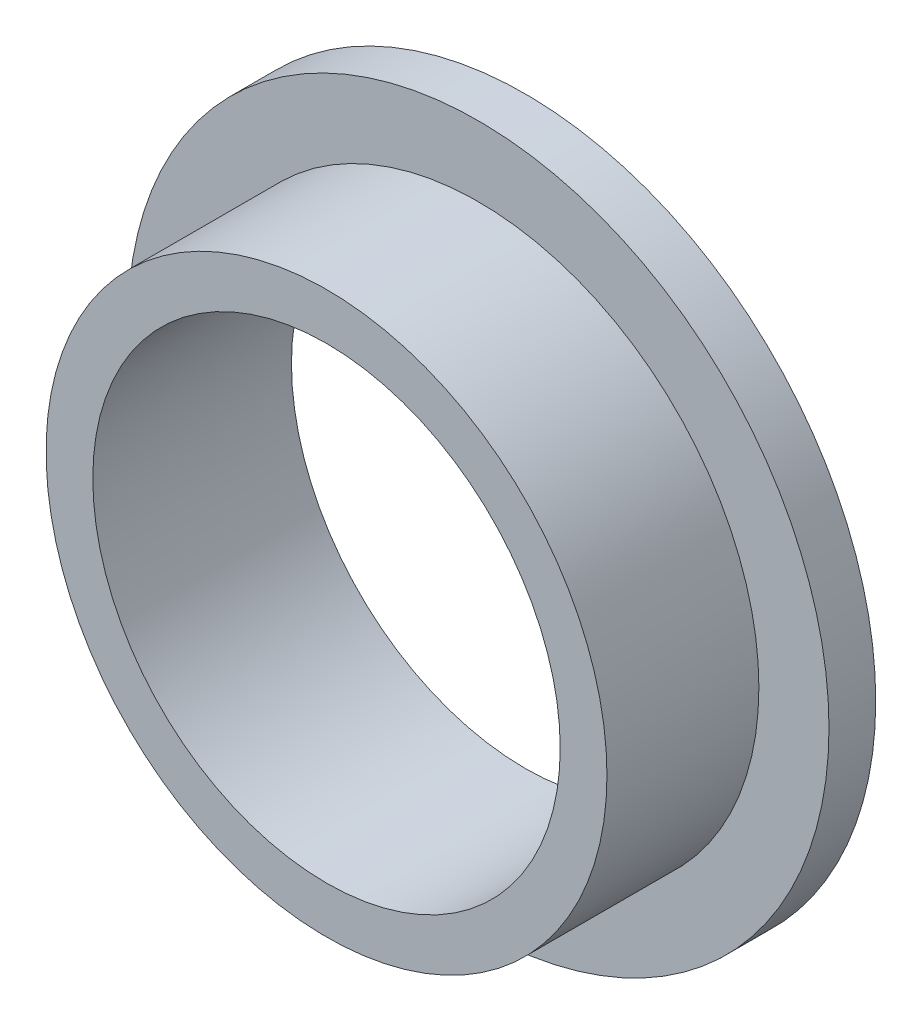
SolidWorks part; units mm, degrees
ref_plane "Front Plane" through (0, 0, 0) normal (0, 0, 1) x (1, 0, 0)
ref_plane "Top Plane" through (0, 0, 0) normal (0, 1, 0) x (1, 0, 0)
ref_plane "Right Plane" through (0, 0, 0) normal (1, 0, 0) x (0, 0, -1)
sketch "Sketch1" plane through (0, 0, 0) normal (1, 0, 0) x (0, 0, -1)
  line L0 (-30.7627, 0) -> (32.4153, 0) construction
  line L1 (0, 0) -> (0, 30) construction
  line L2 (-25.5, 30) -> (0, 30)
  line L3 (0, 30) -> (0, 45)
  line L4 (-25.5, 36) -> (-6, 36)
  line L5 (-6, 36) -> (-6, 45)
  line L6 (-6, 45) -> (0, 45)
  line L7 (-25.5, 36) -> (-25.5, 30)
  dimension "D1" = 90
  dimension "D2" = 60
  dimension "D3" = 25.5
  dimension "D4" = 6
revolve "Revolve1" add sketch "Sketch1" angle 360 about L0
